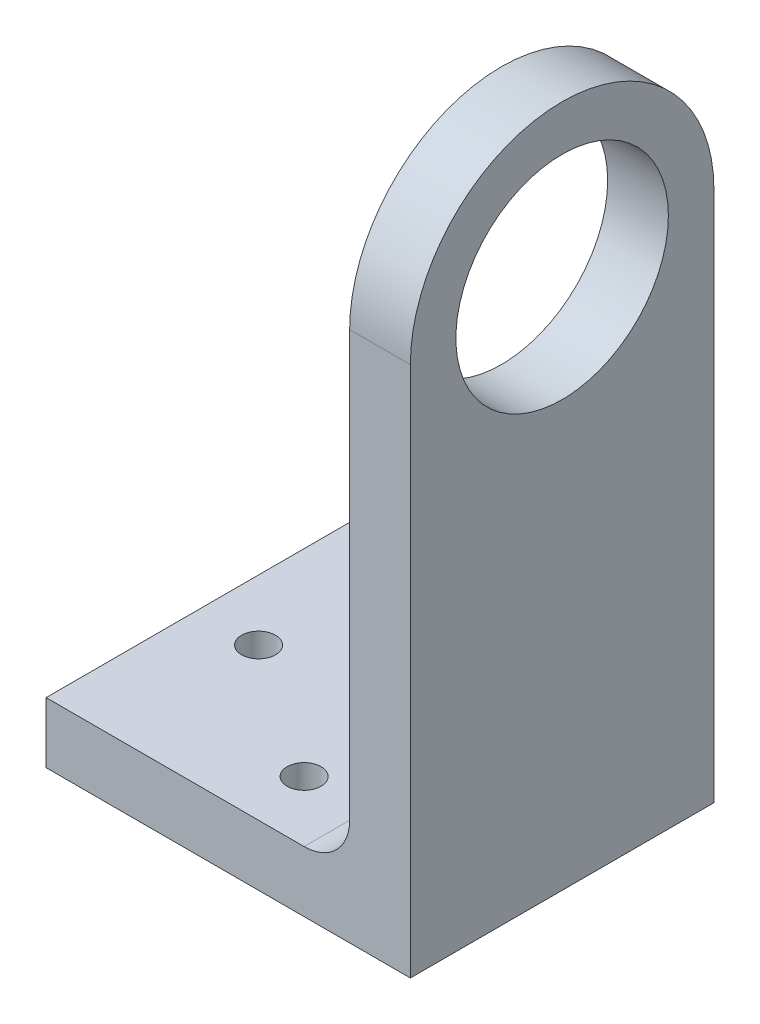
SolidWorks part; units mm, degrees
ref_plane "Front Plane" through (0, 0, 0) normal (0, 0, 1) x (1, 0, 0)
ref_plane "Top Plane" through (0, 0, 0) normal (0, 1, 0) x (1, 0, 0)
ref_plane "Right Plane" through (0, 0, 0) normal (1, 0, 0) x (0, 0, -1)
sketch "Sketch3" plane through (0, 0, 0) normal (1, 0, 0) x (0, 0, -1)
  line L1 (0, 0) -> (31.75, 0)
  line L2 (0, 0) -> (0, 49.2125)
  line L4 (31.75, 0) -> (31.75, 49.2125)
  circle A4 centre (15.875, 49.2125) radius 11.1125
  arc A5 (0, 49.2125) -> (31.75, 49.2125) centre (15.875, 49.2125) cw
  point P34 (15.875, 0)
  dimension "D4" = 22.225
  dimension "D1" = 49.2125
  dimension "D2" = 31.75
extrude "Boss-Extrude1" add sketch "Sketch3" along normal blind 6.35
sketch "Sketch5" plane through (6.35, 0, 0) normal (1, 0, 0) x (0, 0, -1)
  line L1 (0, 0) -> (31.75, 0)
  line L2 (0, 0) -> (0, -6.35)
  line L3 (0, -6.35) -> (31.75, -6.35)
  line L4 (31.75, 0) -> (31.75, -6.35)
  dimension "D1" = 6.35
extrude "Boss-Extrude2" add sketch "Sketch5" against normal blind 38.1
fillet "Fillet1" radius 4.7625 1 edges at (0, 0, -15.875)
sketch "Sketch6" plane through (0, 0, 0) normal (0, 1, 0) x (1, 0, 0)
  line L0 (-31.75, 0) -> (-4.7625, 0) construction
  line L1 (-4.7625, 0) -> (-4.7625, 31.75) construction
  line L2 (-31.75, 31.75) -> (-31.75, 0) construction
  line L3 (0, 15.875) -> (-33.0413, 15.875) construction
  line L4 (0, 31.75) -> (0, 0) construction
  circle A0 centre (-11.1125, 6.35) radius 1.777
  circle A2 centre (-25.4, 15.875) radius 1.777
  circle A3 centre (-11.1125, 25.4) radius 1.777
  dimension "D1" = 3.554
  dimension "D2" = 6.35
  dimension "D3" = 6.35
  dimension "D4" = 6.35
extrude "Cut-Extrude1" cut sketch "Sketch6" against normal through all
equation "\"D1@Sketch6\" = 3.3mm + \"normtol\""
equation "\"tighttol\" = 0.005in"
equation "\"normtol\" = 0.01in"
equation "\"loosetol\" = 0.02in"
equation "\"Fry height\"= 0.5in"
equation "\"Fry spacing\"= 0.5625in"
equation "\"Potato width\"= \"Fry spacing\" * 4"
equation "\"Potato length\"= 80mm"
equation "\"top robot surface separation\" = 0.6875"
equation "\"D1@Sketch3\"=1.25+\"top robot surface separation\""
